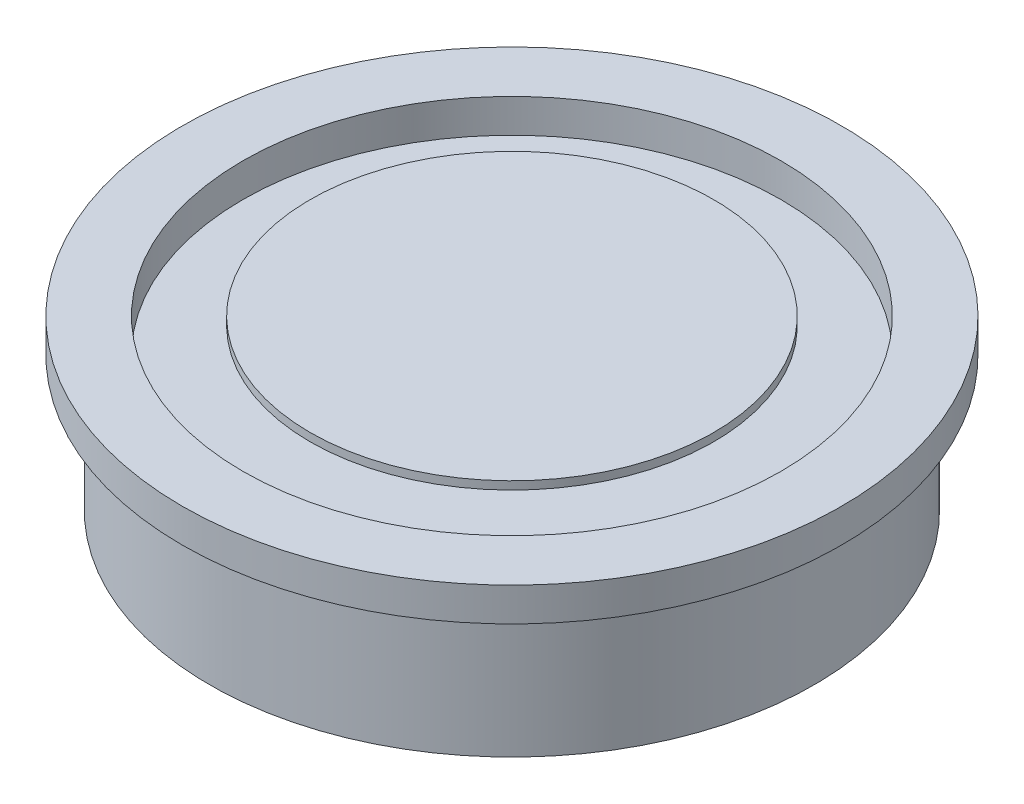
SolidWorks part; units mm, degrees
ref_plane "Front Plane" through (0, 0, 0) normal (0, 0, 1) x (1, 0, 0)
ref_plane "Top Plane" through (0, 0, 0) normal (0, 1, 0) x (1, 0, 0)
ref_plane "Right Plane" through (0, 0, 0) normal (1, 0, 0) x (0, 0, -1)
ref_plane "Plane1" through (0, 0, 0) normal (0, 0, -1) x (-1, 0, 0)
sketch "Sketch1" plane through (0, 0, 0) normal (0, 0, -1) x (-1, 0, 0)
  line L0 (-15.5575, 6.35) -> (0, 6.35)
  line L1 (0, 6.35) -> (0, 7.9375)
  line L2 (0, 7.9375) -> (-15.5575, 7.9375)
  line L3 (-15.5575, 7.9375) -> (-15.5575, 6.35)
  line L4 (0, 6.35) -> (0, 7.9375) construction
revolve "Revolve1" add sketch "Sketch1" angle 360 about L4
hole_wizard "M22 Clearance Hole1" positions "Sketch3" profile "Sketch2" hole size "M22" standard "ANSI Metric"
sketch "Sketch3" plane through (0, 7.9375, 0) normal (0, 1, 0) x (1, 0, 0)
  point P0 (0, 0)
sketch "Sketch2" plane through (0, 7.9375, 0) normal (1, 0, 0) x (0, 0, 1)
  line L0 (0, 0) -> (0, 1.5875)
  line L1 (0, 1.5875) -> (12.7, 1.5875)
  line L2 (12.7, 1.5875) -> (12.7, 0)
  line L5 (12.7, 0) -> (0, 0)
  line L11 (0, -6.35) -> (0, 107.95) construction
  dimension "Thru Hole Dia." = 25.4
  dimension "Thru Hole Depth" = 1.5875
ref_plane "Plane2" through (0, 7.5565, 0) normal (0, -1, 0) x (1, 0, 0)
sketch "Sketch4" plane through (0, 7.5565, 0) normal (0, -1, 0) x (1, 0, 0)
  circle A0 centre (0, 0) radius 9.525
extrude "Boss-Extrude1" add sketch "Sketch4" against normal blind 0.381
sketch "Sketch5" plane through (0, 6.35, 0) normal (0, -1, 0) x (1, 0, 0)
  circle A0 centre (0, 0) radius 14.2748
extrude "Boss-Extrude2" add sketch "Sketch5" along normal blind 6.35
sketch "Sketch6" plane through (0, 0, 0) normal (0, -1, 0) x (1, 0, 0)
  line L0 (-3.6719, 6.36) -> (-7.3439, 0)
  line L1 (-7.3439, 0) -> (-3.6719, -6.36)
  line L2 (-3.6719, -6.36) -> (3.6719, -6.36)
  line L3 (3.6719, -6.36) -> (7.3439, 0)
  line L4 (7.3439, 0) -> (3.6719, 6.36)
  line L5 (3.6719, 6.36) -> (-3.6719, 6.36)
extrude "Cut-Extrude1" cut sketch "Sketch6" against normal up to next (6.35 mm away)
